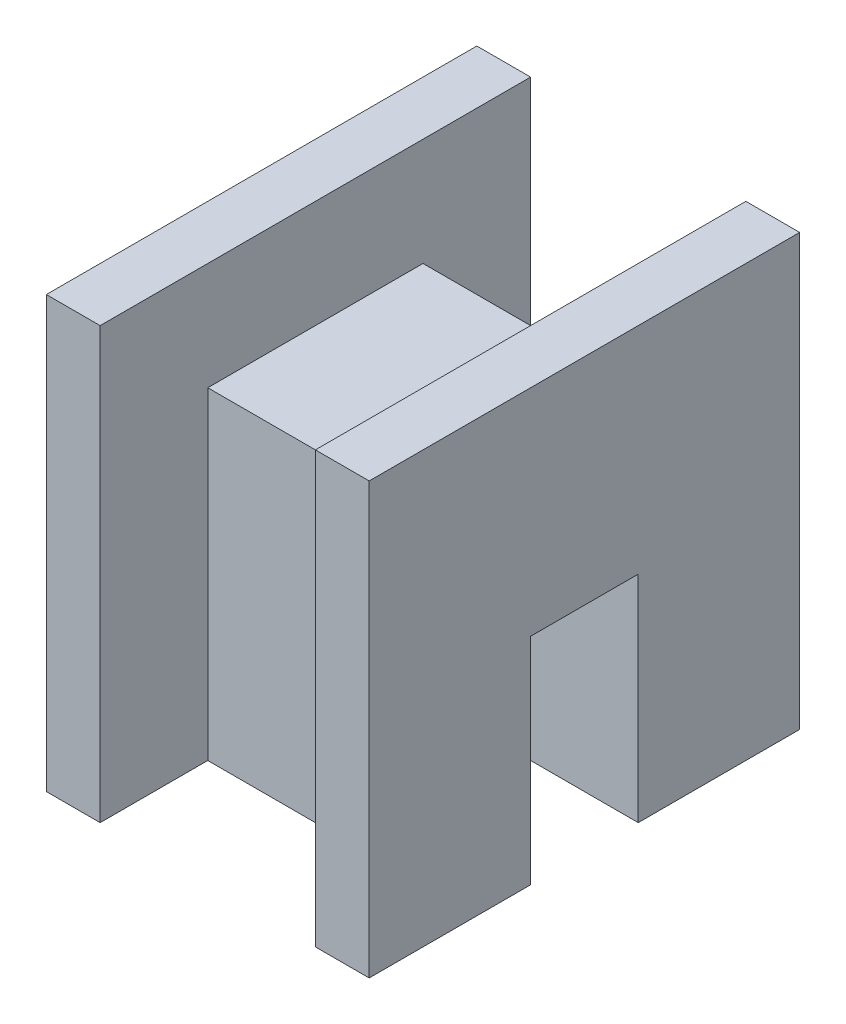
SolidWorks part; units mm, degrees
material "AISI 1020"
ref_plane "Plano frontal" through (0, 0, 0) normal (0, 0, 1) x (1, 0, 0)
ref_plane "Plano superior" through (0, 0, 0) normal (0, 1, 0) x (1, 0, 0)
ref_plane "Plano direito" through (0, 0, 0) normal (1, 0, 0) x (0, 0, -1)
sketch "Esboço1" plane through (0, 0, 0) normal (1, 0, 0) x (0, 0, -1)
  line L0 (-20, 0) -> (-20, 40)
  line L1 (-20, 40) -> (20, 40)
  line L2 (20, 40) -> (20, 0)
  line L3 (20, 0) -> (5, 0)
  line L4 (5, 0) -> (5, 20)
  line L5 (5, 20) -> (-5, 20)
  line L6 (-5, 20) -> (-5, 0)
  line L7 (-5, 0) -> (-20, 0)
  point P6 (0, 0)
  point P9 (0, 0)
  point P11 (0, 20)
  dimension "D1" = 40
  dimension "D2" = 40
  dimension "D3" = 20
  dimension "D4" = 10
extrude "Ressalto-extrusão1" add sketch "Esboço1" along normal mid plane 30
sketch "Esboço2" plane through (0, 0, 0) normal (1, 0, 0) x (0, 0, -1)
  line L0 (-10, 0) -> (-10, 30)
  line L1 (-20, 0) -> (-5, 0) construction
  line L2 (-10, 30) -> (10, 30)
  line L3 (10, 30) -> (10, 0)
  line L4 (5, 0) -> (20, 0) construction
  line L5 (10, 0) -> (5, 0) construction
  line L6 (-10, 0) -> (-20, 0)
  line L7 (-20, 0) -> (-20, 40)
  line L8 (-20, 40) -> (20, 40)
  line L9 (20, 40) -> (20, 0)
  line L10 (20, 0) -> (10, 0)
  line L11 (0, 20) -> (0, 30) construction
  line L12 (-5, 20) -> (5, 20) construction
  dimension "D1" = 20
  dimension "D2" = 10
extrude "Corte-extrusão1" cut sketch "Esboço2" against normal mid plane 20
